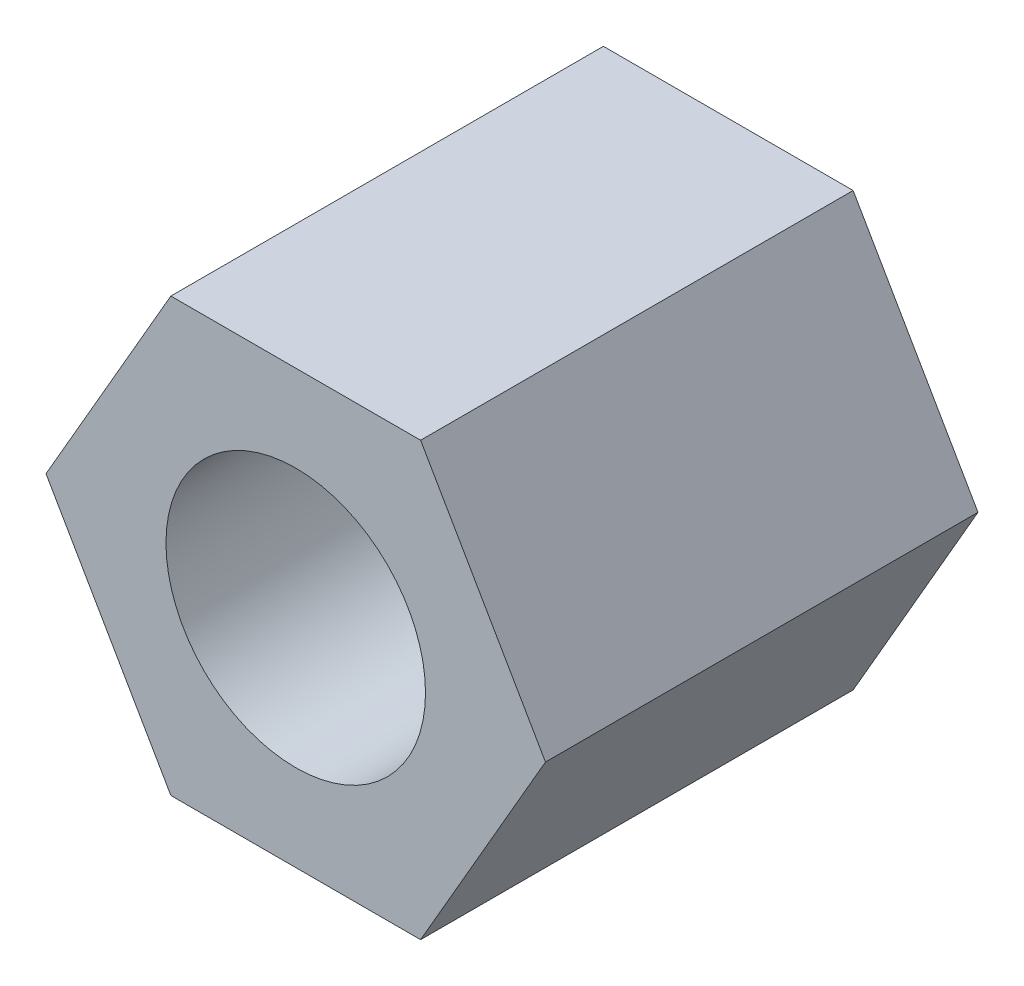
SolidWorks part; units mm, degrees
material "AISI 304"
ref_plane "前视基准面" through (0, 0, 0) normal (0, 0, 1) x (1, 0, 0)
ref_plane "上视基准面" through (0, 0, 0) normal (0, 1, 0) x (1, 0, 0)
ref_plane "右视基准面" through (0, 0, 0) normal (1, 0, 0) x (0, 0, -1)
sketch "草图1" plane through (0, 0, 0) normal (0, 0, 1) x (1, 0, 0)
  line L1 (1.4434, -2.5) -> (2.8868, 0)
  line L2 (2.8868, 0) -> (1.4434, 2.5)
  line L3 (1.4434, 2.5) -> (-1.4434, 2.5)
  line L4 (-1.4434, 2.5) -> (-2.8868, 0)
  line L5 (-2.8868, 0) -> (-1.4434, -2.5)
  line L6 (-1.4434, -2.5) -> (1.4434, -2.5)
  circle A0 centre (0, 0) radius 2.5 construction
  circle A1 centre (0, 0) radius 1.5
  dimension "D1" = 3
  dimension "D2" = 5
extrude "凸台-拉伸1" add sketch "草图1" along normal blind 5
